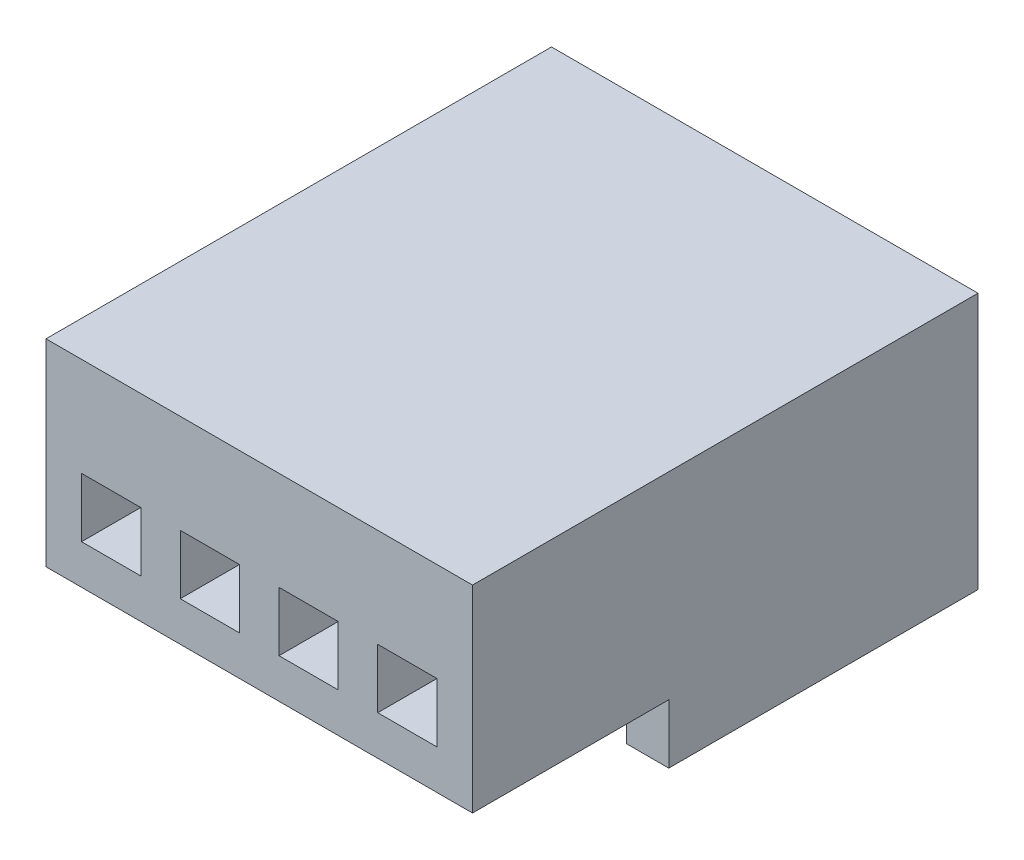
SolidWorks part; units mm, degrees
ref_plane "Front" through (0, 0, 0) normal (0, 0, 1) x (1, 0, 0)
ref_plane "Top" through (0, 0, 0) normal (0, 1, 0) x (1, 0, 0)
ref_plane "Right" through (0, 0, 0) normal (1, 0, 0) x (0, 0, -1)
sketch "草圖1" plane through (0, 0, 0) normal (0, 1, 0) x (1, 0, 0)
  line L1 (-5.4, 0) -> (5.4, 0)
  line L2 (-5.4, 0) -> (-5.4, 12.8)
  line L3 (-5.4, 12.8) -> (5.4, 12.8)
  line L4 (5.4, 0) -> (5.4, 12.8)
  dimension "D1" = 10.8
  dimension "D2" = 12.8
extrude "填料-伸長1" add sketch "草圖1" along normal blind 5
sketch "草圖2" plane through (0, 0, -12.8) normal (0, 0, -1) x (-1, 0, 0)
  line L0 (-5.4, 5) -> (-5.4, 0) construction
  line L1 (-4.5, 2.5) -> (-3, 2.5)
  line L2 (-4.5, 2.5) -> (-4.5, 1)
  line L3 (-4.5, 1) -> (-3, 1)
  line L4 (-3, 2.5) -> (-3, 1)
  line L5 (-2, 2.5) -> (-0.5, 2.5)
  line L6 (-2, 2.5) -> (-2, 1)
  line L7 (-2, 1) -> (-0.5, 1)
  line L8 (-0.5, 2.5) -> (-0.5, 1)
  line L9 (0.5, 2.5) -> (2, 2.5)
  line L10 (0.5, 2.5) -> (0.5, 1)
  line L11 (0.5, 1) -> (2, 1)
  line L12 (2, 2.5) -> (2, 1)
  line L13 (3, 2.5) -> (4.5, 2.5)
  line L14 (3, 2.5) -> (3, 1)
  line L15 (3, 1) -> (4.5, 1)
  line L16 (4.5, 2.5) -> (4.5, 1)
  line L17 (5.4, 5) -> (5.4, 0) construction
  line L18 (-5.4, 0) -> (5.4, 0) construction
  point P16 (0.6144, 2.4274)
  point P17 (-0.4692, 2.4274)
  point P18 (0.4468, 2.3939)
  point P19 (2.8822, 2.3604)
  dimension "D1" = 1.5
  dimension "D2" = 1.5
  dimension "D3" = 1.5
  dimension "D4" = 1.5
  dimension "D5" = 1.5
  dimension "D6" = 1
  dimension "D7" = 1
  dimension "D8" = 1
  dimension "D9" = 0.9
  dimension "D10" = 0.9
  dimension "D11" = 1
extrude "除料-伸長1" cut sketch "草圖2" against normal through all
sketch "草圖3" plane through (0, 0, 0) normal (0, -1, 0) x (1, 0, 0)
  line L1 (-5.4, -12.8) -> (-4.4206, -12.8)
  line L2 (-5.4, -12.8) -> (-5.4, -4.9693)
  line L3 (-5.4, -4.9693) -> (-4.4206, -4.9693)
  line L4 (-4.4206, -12.8) -> (-4.4206, -4.9693)
  line L5 (5.4, -12.8) -> (4.3349, -12.8)
  line L6 (5.4, -12.8) -> (5.4, -4.9693)
  line L7 (5.4, -4.9693) -> (4.3349, -4.9693)
  line L8 (4.3349, -12.8) -> (4.3349, -4.9693)
extrude "填料-伸長2" add sketch "草圖3" along normal blind 1.5
